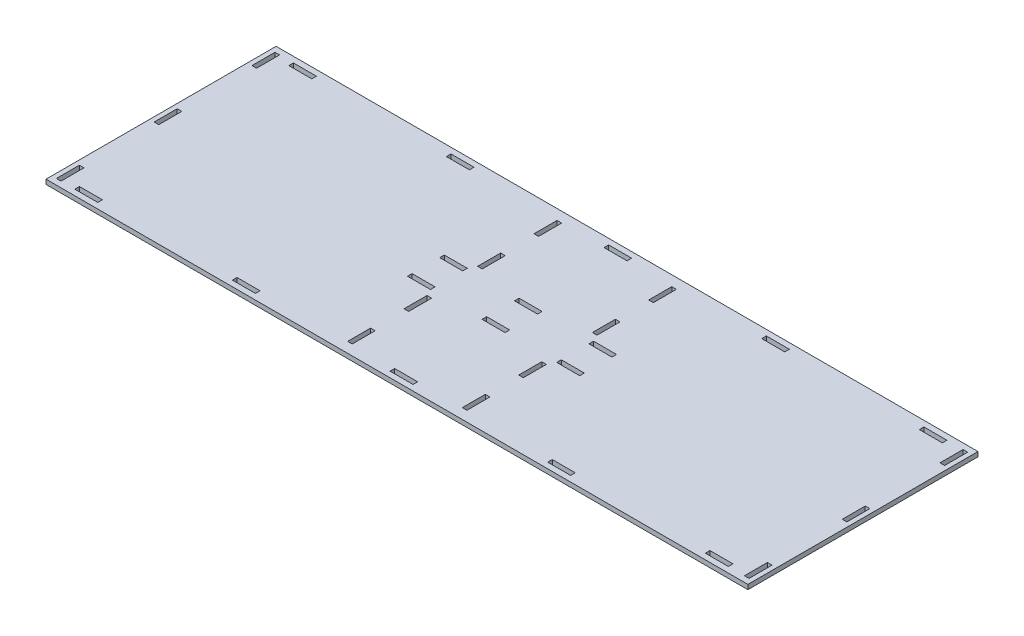
SolidWorks part; units mm, degrees
ref_plane "Front Plane" through (0, 0, 0) normal (0, 0, 1) x (1, 0, 0)
ref_plane "Top Plane" through (0, 0, 0) normal (0, 1, 0) x (1, 0, 0)
ref_plane "Right Plane" through (0, 0, 0) normal (1, 0, 0) x (0, 0, -1)
sketch "Sketch1" plane through (0, 0, 0) normal (0, 1, 0) x (1, 0, 0)
  line L0 (0, 0) -> (0, 189.2154) construction
  line L1 (-305, 100) -> (-305, -100)
  line L2 (-305, -100) -> (305, -100)
  line L4 (-305, 100) -> (305, 100)
  line L6 (-330, -100) -> (330, 100) construction
  line L7 (-330, 100) -> (330, -100) construction
  line L60 (-301, -95) -> (-301, -75)
  line L61 (-301, -95) -> (326, -95) construction
  line L62 (-301, -95) -> (-301, 95) construction
  line L63 (-301, 95) -> (326, 95) construction
  line L65 (-301, -95) -> (326, 95) construction
  line L66 (-301, 95) -> (326, -95) construction
  line L67 (-301, -95) -> (-297, -95)
  line L68 (-301, 95) -> (-297, 95)
  line L69 (-301, -75) -> (-297, -75)
  line L71 (-421.8057, 0) -> (404.5887, 0) construction
  line L72 (-301, 75) -> (-301, 95)
  line L73 (-301, -10) -> (-297, -10)
  line L76 (-301, -10) -> (-301, 10)
  line L77 (-301, 10) -> (-297, 10)
  line L78 (-297, 10) -> (-297, -10)
  line L79 (-301, 75) -> (-297, 75)
  line L91 (-265, 95) -> (-285, 95)
  line L93 (-265, 95) -> (-265, 91)
  line L94 (-148, 95) -> (-128, 95)
  line L95 (-148, 95) -> (-148, 91)
  line L96 (-128, 95) -> (-128, 91)
  line L97 (9, 95) -> (9, 91)
  line L98 (-11, 95) -> (-11, 91)
  line L99 (-265, 91) -> (-285, 91)
  line L100 (-148, 91) -> (-128, 91)
  line L101 (9, 91) -> (-11, 91)
  line L104 (9, 95) -> (-11, 95)
  line L128 (9, -95) -> (-11, -95)
  line L129 (9, -95) -> (9, -91)
  line L131 (-11, -95) -> (-11, -91)
  line L132 (-148, -95) -> (-148, -91)
  line L133 (-148, -91) -> (-128, -91)
  line L134 (-128, -95) -> (-128, -91)
  line L135 (-148, -95) -> (-128, -95)
  line L136 (-265, -95) -> (-265, -91)
  line L137 (-265, -91) -> (-285, -91)
  line L139 (-265, -95) -> (-285, -95)
  line L143 (-74.8597, -12) -> (-74.8597, 12) construction
  line L144 (-74.8597, 0) -> (0, 0) construction
  line L145 (-47.8597, -91) -> (-47.8597, -71)
  line L147 (-51.8597, -91) -> (-51.8597, -71)
  line L148 (-47.8597, -71) -> (-51.8597, -71)
  line L149 (-51.8597, -42) -> (-51.8597, -22)
  line L150 (-51.8597, -42) -> (-47.8597, -42)
  line L151 (-47.8597, -42) -> (-47.8597, -22)
  line L152 (-51.8597, -22) -> (-47.8597, -22)
  line L161 (-74.8597, -16) -> (-74.8597, -12)
  line L162 (-74.8597, -16) -> (-54.8597, -16)
  line L163 (-54.8597, -16) -> (-54.8597, -12)
  line L164 (-74.8597, -12) -> (-54.8597, -12)
  line L165 (-74.8597, 12) -> (-74.8597, 16)
  line L166 (-74.8597, 12) -> (-54.8597, 12)
  line L167 (-54.8597, 12) -> (-54.8597, 16)
  line L168 (-74.8597, 16) -> (-54.8597, 16)
  line L169 (-51.8597, 22) -> (-51.8597, 42)
  line L170 (-51.8597, 22) -> (-47.8597, 22)
  line L171 (-47.8597, 22) -> (-47.8597, 42)
  line L172 (-51.8597, 42) -> (-47.8597, 42)
  line L177 (-10, -16) -> (-10, -12)
  line L178 (-10, -16) -> (10, -16)
  line L179 (10, -16) -> (10, -12)
  line L180 (-10, -12) -> (10, -12)
  line L181 (-9.8597, 12) -> (-9.8597, 16)
  line L182 (-9.8597, 12) -> (10.1403, 12)
  line L183 (10.1403, 12) -> (10.1403, 16)
  line L184 (-9.8597, 16) -> (10.1403, 16)
  line L201 (305, 100) -> (305, -100)
  line L202 (-297, 189.2154) -> (-297, -166.9381) construction
  line L204 (-285, 95) -> (-285, 91)
  line L205 (-297, 75) -> (-297, 95)
  line L206 (-285, -91) -> (-285, -95)
  line L208 (-297, -75) -> (-297, -95)
  line L210 (126, 95) -> (126, 91)
  line L211 (126, 91) -> (146, 91)
  line L212 (146, 91) -> (146, 95)
  line L213 (146, 95) -> (126, 95)
  line L214 (263, 95) -> (263, 91)
  line L215 (263, 91) -> (283, 91)
  line L216 (283, 91) -> (283, 95)
  line L222 (263, 95) -> (283, 95)
  line L223 (-51.8597, -91) -> (-47.8597, -91)
  line L224 (9, -91) -> (-11, -91)
  line L225 (51.8597, -91) -> (47.8597, -91)
  line L226 (47.8597, -91) -> (47.8597, -71)
  line L227 (47.8597, -71) -> (51.8597, -71)
  line L228 (51.8597, -91) -> (51.8597, -71)
  line L229 (51.8597, -42) -> (47.8597, -42)
  line L230 (47.8597, -42) -> (47.8597, -22)
  line L231 (51.8597, -22) -> (47.8597, -22)
  line L232 (51.8597, -42) -> (51.8597, -22)
  line L233 (74.8597, -16) -> (54.8597, -16)
  line L234 (54.8597, -16) -> (54.8597, -12)
  line L235 (74.8597, -12) -> (54.8597, -12)
  line L236 (74.8597, -16) -> (74.8597, -12)
  line L237 (74.8597, 12) -> (54.8597, 12)
  line L238 (54.8597, 12) -> (54.8597, 16)
  line L239 (74.8597, 16) -> (54.8597, 16)
  line L240 (74.8597, 12) -> (74.8597, 16)
  line L241 (51.8597, 22) -> (47.8597, 22)
  line L242 (47.8597, 22) -> (47.8597, 42)
  line L243 (51.8597, 42) -> (47.8597, 42)
  line L244 (51.8597, 22) -> (51.8597, 42)
  line L245 (263, -95) -> (263, -91)
  line L246 (263, -91) -> (283, -91)
  line L247 (283, -91) -> (283, -95)
  line L248 (263, -95) -> (283, -95)
  line L249 (146, -91) -> (146, -95)
  line L250 (126, -91) -> (146, -91)
  line L251 (126, -95) -> (126, -91)
  line L252 (146, -95) -> (126, -95)
  line L253 (51.8597, 91) -> (51.8597, 71)
  line L254 (47.8597, 71) -> (51.8597, 71)
  line L255 (47.8597, 91) -> (47.8597, 71)
  line L256 (51.8597, 91) -> (47.8597, 91)
  line L257 (-51.8597, 91) -> (-47.8597, 91)
  line L258 (-47.8597, 91) -> (-47.8597, 71)
  line L259 (-47.8597, 71) -> (-51.8597, 71)
  line L260 (-51.8597, 91) -> (-51.8597, 71)
  line L261 (301, 75) -> (297, 75)
  line L262 (301, 75) -> (301, 95)
  line L263 (301, 95) -> (297, 95)
  line L264 (297, 75) -> (297, 95)
  line L265 (301, -10) -> (301, 10)
  line L266 (301, 10) -> (297, 10)
  line L267 (297, 10) -> (297, -10)
  line L268 (301, -10) -> (297, -10)
  line L269 (301, -75) -> (297, -75)
  line L270 (301, -95) -> (301, -75)
  line L271 (301, -95) -> (297, -95)
  line L272 (297, -75) -> (297, -95)
  point P63 (-299, -95)
  dimension "D2" = 200
  dimension "D3" = 8
  dimension "D4" = 190
  dimension "D5" = 20
  dimension "D6" = 20
  dimension "D7" = 20
  dimension "D8" = 10
  dimension "D9" = 20
  dimension "D10" = 5
  dimension "D11" = 20
  dimension "D12" = 20
  dimension "D13" = 610
  dimension "D14" = 117
  dimension "D15" = 117
  dimension "D16" = 20
  dimension "D17" = 4
  dimension "D18" = 4
  dimension "D19" = 4
  dimension "D20" = 117
  dimension "D21" = 20
  dimension "D22" = 117
  dimension "D23" = 20
  dimension "D24" = 4
  dimension "D25" = 253.1403
  dimension "D26" = 20
  dimension "D27" = 9
  dimension "D28" = 20
  dimension "D29" = 29
extrude "Boss-Extrude1" add sketch "Sketch1" along normal blind 4
